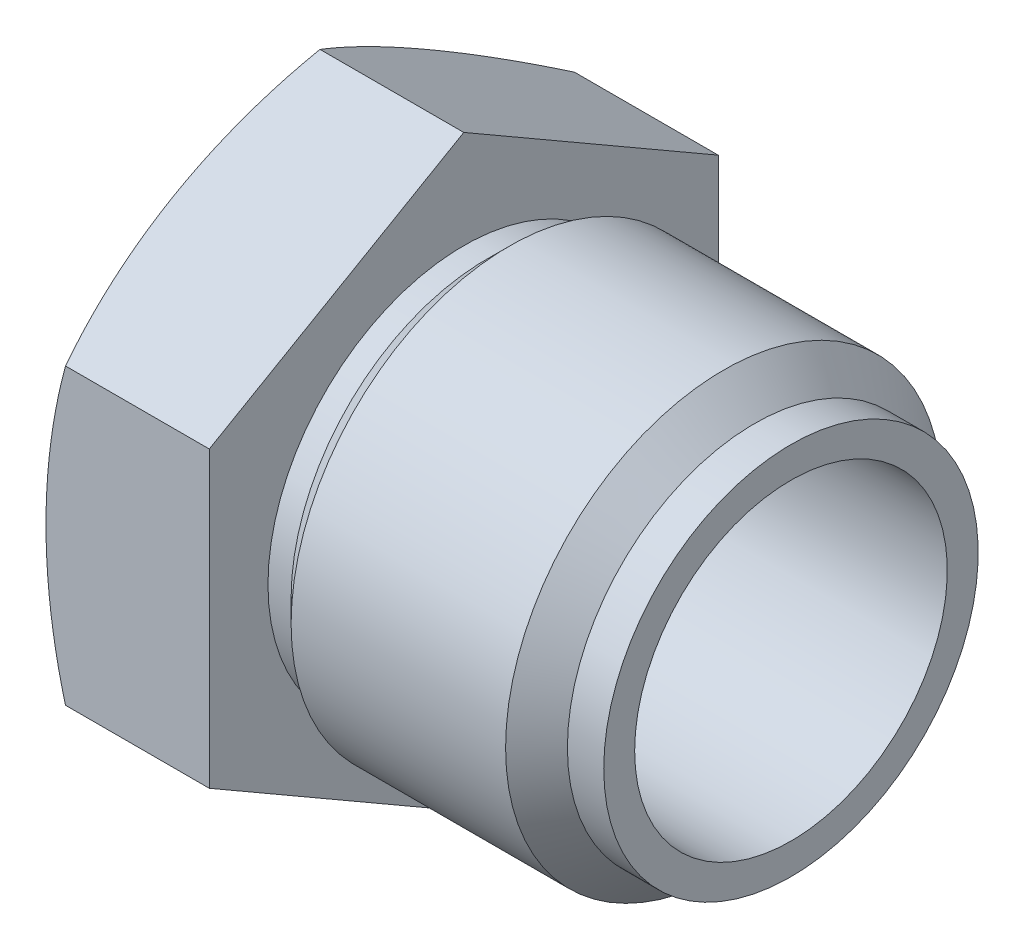
SolidWorks part; units mm, degrees
ref_plane "Front Plane" through (0, 0, 0) normal (0, 0, 1) x (1, 0, 0)
ref_plane "Top Plane" through (0, 0, 0) normal (0, 1, 0) x (1, 0, 0)
ref_plane "Right Plane" through (0, 0, 0) normal (1, 0, 0) x (0, 0, -1)
ref_plane "Plane1" through (0, 0, 0) normal (0, 0, 1) x (1, 0, 0)
sketch "Sketch1" plane through (0, 0, 0) normal (0, 0, 1) x (1, 0, 0)
  line L0 (-2.4907, 10) -> (0, 10)
  line L1 (0, 10) -> (0, 5.3865)
  line L2 (0, 5.3865) -> (0.6365, 5.3865)
  line L3 (0.6365, 5.3865) -> (1.25, 6)
  line L4 (1.25, 6) -> (7.15, 6)
  line L5 (7.15, 6) -> (8, 5.15)
  line L6 (8, 5.15) -> (9, 5.15)
  line L7 (9, 5.15) -> (9, 0)
  line L8 (9, 0) -> (-6, 0)
  line L9 (9, 0) -> (-6, 0) construction
  arc A0 (-6, 0) -> (-2.8995, 9.7879) centre (11, 0) cw
  arc A1 (-2.8995, 9.7879) -> (-2.4907, 10) centre (-2.4907, 9.5) cw
revolve "Revolve1" add sketch "Sketch1" angle 360 about L9
cosmetic thread "Cosmetic Thread1" parameters "D1"=7.127, "D2"=10.773
ref_plane "Plane2" through (0, 0, 0) normal (0, 0, 1) x (1, 0, 0)
sketch "Sketch2" plane through (0, 0, 0) normal (0, 0, 1) x (1, 0, 0)
  line L0 (-1.6, 0) -> (-1.6, 4.3)
  line L1 (-1.6, 4.3) -> (9, 4.3)
  line L2 (9, 4.3) -> (9, 0)
  line L3 (9, 0) -> (-1.6, 0)
  line L4 (9, 0) -> (-1.6, 0) construction
revolve "Cut-Revolve1" cut sketch "Sketch2" angle 360 about L4
ref_plane "Plane3" through (-6, 0, 0) normal (1, 0, 0) x (0, 0, -1)
sketch "Sketch3" plane through (-6, 0, 0) normal (1, 0, 0) x (0, 0, -1)
  line L0 (-20, -20) -> (20, -20)
  line L1 (20, -20) -> (20, 20)
  line L2 (20, 20) -> (-20, 20)
  line L3 (-20, 20) -> (-20, -20)
  line L4 (-7, -4.0415) -> (0, -8.0829)
  line L5 (0, -8.0829) -> (7, -4.0415)
  line L6 (7, -4.0415) -> (7, 4.0415)
  line L7 (7, 4.0415) -> (0, 8.0829)
  line L8 (0, 8.0829) -> (-7, 4.0415)
  line L9 (-7, 4.0415) -> (-7, -4.0415)
extrude "Cut-Extrude1" cut sketch "Sketch3" along normal blind 6.5
ref_plane "Plane4" through (-6, 0, 0) normal (1, 0, 0) x (0, 0, -1)
sketch "Sketch4" plane through (-6, 0, 0) normal (1, 0, 0) x (0, 0, -1)
  line L0 (-2.1894, -0.4503) -> (-1.4536, -0.8416)
  line L1 (-1.4536, -0.8416) -> (-0.8521, -0.8521)
  line L2 (-0.8521, -0.8521) -> (-0.8416, -1.4536)
  line L3 (-0.8416, -1.4536) -> (-0.4503, -2.1894)
  line L4 (0.4503, -2.1894) -> (0.8416, -1.4536)
  line L5 (0.8416, -1.4536) -> (0.8521, -0.8521)
  line L6 (0.8521, -0.8521) -> (1.4536, -0.8416)
  line L7 (1.4536, -0.8416) -> (2.1894, -0.4503)
  line L8 (2.1894, 0.4503) -> (1.4536, 0.8416)
  line L9 (1.4536, 0.8416) -> (0.8521, 0.8521)
  line L10 (0.8521, 0.8521) -> (0.8416, 1.4536)
  line L11 (0.8416, 1.4536) -> (0.4503, 2.1894)
  line L12 (-0.4503, 2.1894) -> (-0.8416, 1.4536)
  line L13 (-0.8416, 1.4536) -> (-0.8521, 0.8521)
  line L14 (-0.8521, 0.8521) -> (-1.4536, 0.8416)
  line L15 (-1.4536, 0.8416) -> (-2.1894, 0.4503)
  arc A0 (-2.1894, 0.4503) -> (-2.1894, -0.4503) centre (-1.95, 0) ccw
  arc A1 (-0.4503, -2.1894) -> (0.4503, -2.1894) centre (0, -1.95) ccw
  arc A2 (2.1894, -0.4503) -> (2.1894, 0.4503) centre (1.95, 0) ccw
  arc A3 (0.4503, 2.1894) -> (-0.4503, 2.1894) centre (0, 1.95) ccw
extrude "Cut-Extrude2" cut sketch "Sketch4" along normal blind 2.29
ref_plane "Plane5" through (-6, 0, 0) normal (1, 0, 0) x (0, 0, -1)
sketch "Sketch5" plane through (-6, 0, 0) normal (1, 0, 0) x (0, 0, -1)
  line L0 (-0.95, -5.4) -> (0.95, -5.4)
  line L1 (0.95, -5.4) -> (0.95, 5.4)
  line L2 (0.95, 5.4) -> (-0.95, 5.4)
  line L3 (-0.95, 5.4) -> (-0.95, -5.4)
extrude "Cut-Extrude3" cut sketch "Sketch5" along normal blind 1.4
